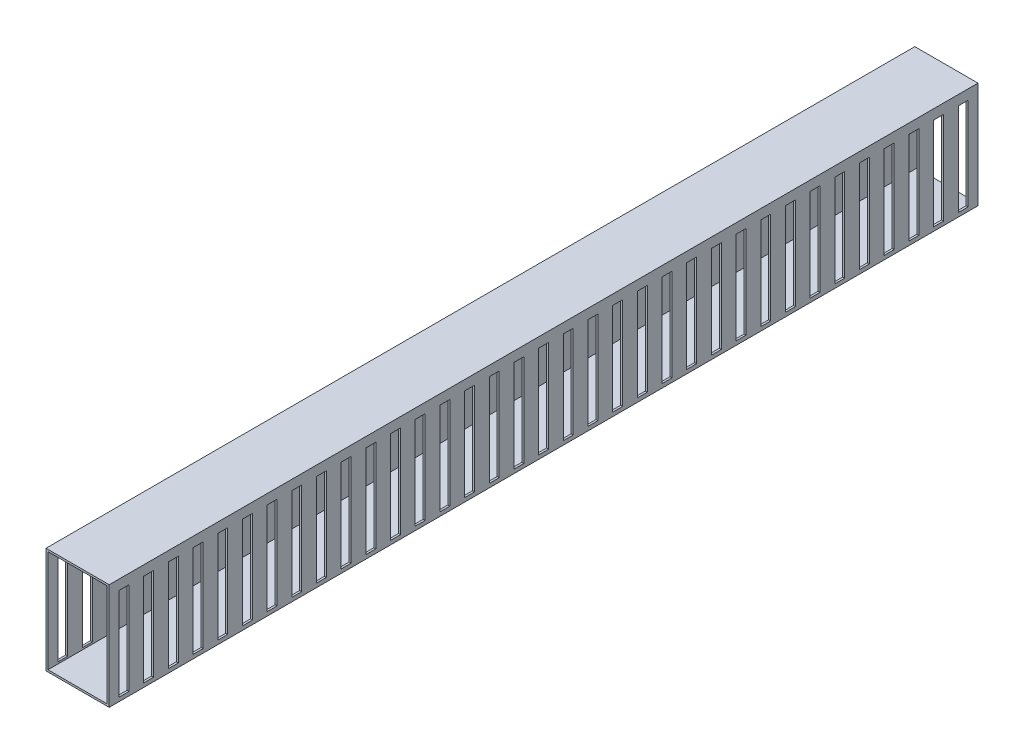
SolidWorks part; units mm, degrees
ref_plane "Plan de face" through (0, 0, 0) normal (0, 0, 1) x (1, 0, 0)
ref_plane "Plan de dessus" through (0, 0, 0) normal (0, 1, 0) x (1, 0, 0)
ref_plane "Plan de droite" through (0, 0, 0) normal (1, 0, 0) x (0, 0, -1)
sketch "Esquisse1" plane through (0, 0, 0) normal (0, 0, 1) x (1, 0, 0)
  line L0 (-12.0229, 36.1361) -> (-12.0229, -15.6639)
  line L1 (-13.0229, 37.1361) -> (18.9771, 37.1361)
  line L2 (-13.0229, 37.1361) -> (-13.0229, -16.6639)
  line L3 (-13.0229, -16.6639) -> (18.9771, -16.6639)
  line L4 (18.9771, 37.1361) -> (18.9771, -16.6639)
  line L5 (-12.0229, -15.6639) -> (17.9771, -15.6639)
  line L6 (17.9771, 36.1361) -> (17.9771, -15.6639)
  line L7 (-12.0229, 36.1361) -> (17.9771, 36.1361)
  dimension "D1" = 32
  dimension "D2" = 53.8
  dimension "D3" = 1
extrude "Boss.-Extru.1" add sketch "Esquisse1" along normal blind 440
sketch "Esquisse2" plane through (18.9771, 0, 0) normal (1, 0, 0) x (0, 0, -1)
  line L0 (-440, -16.6639) -> (0, -16.6639) construction
  line L1 (-5, -14.6639) -> (-10, -14.6639)
  line L2 (-5, -14.6639) -> (-5, 32.1361)
  line L3 (-5, 32.1361) -> (-10, 32.1361)
  line L4 (-10, -14.6639) -> (-10, 32.1361)
  line L5 (0, -16.6639) -> (0, 37.1361) construction
  line L6 (-440, 37.1361) -> (0, 37.1361) construction
  dimension "D1" = 2
  dimension "D2" = 5
  dimension "D3" = 5
  dimension "D4" = 5
extrude "Enlèv. mat.-Extru.1" cut sketch "Esquisse2" against normal up to surface (32 mm away) up to face at (-13.0229, 10.2361, 220)
pattern_linear "Répétition linéaire1" count 35 spacing 12.5 along (0, 0, 1) of "Enlèv. mat.-Extru.1"
